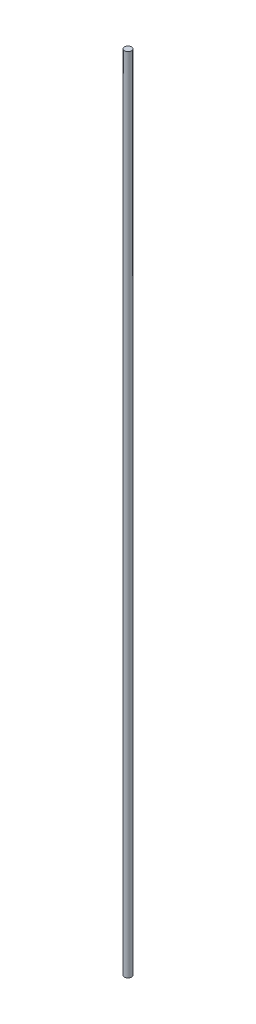
SolidWorks part; units mm, degrees
ref_plane "Спереди" through (0, 0, 0) normal (0, 0, 1) x (1, 0, 0)
ref_plane "Сверху" through (0, 0, 0) normal (0, 1, 0) x (1, 0, 0)
ref_plane "Справа" through (0, 0, 0) normal (1, 0, 0) x (0, 0, -1)
sketch "Эскиз1" plane through (0, 0, 0) normal (0, 1, 0) x (1, 0, 0)
  circle A0 centre (0, 0) radius 4
  dimension "D1" = 8
extrude "Бобышка-Вытянуть1" add sketch "Эскиз1" along normal blind 915
